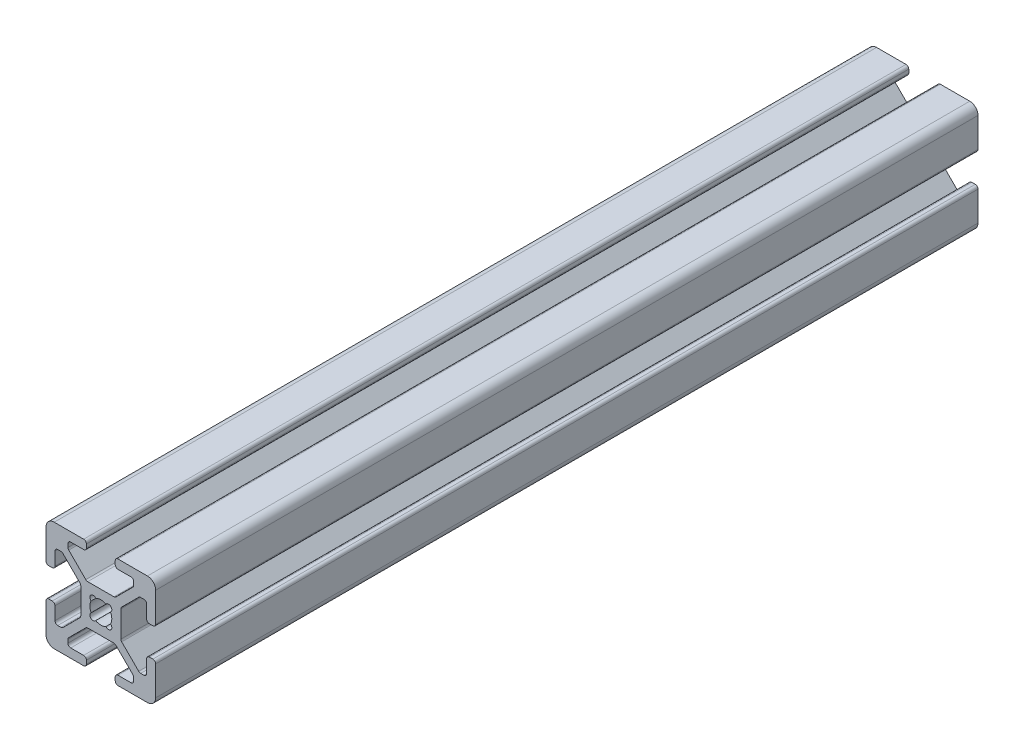
SolidWorks part; units mm, degrees
ref_plane "Front Plane" through (0, 0, 0) normal (0, 0, 1) x (1, 0, 0)
ref_plane "Top Plane" through (0, 0, 0) normal (0, 1, 0) x (1, 0, 0)
ref_plane "Right Plane" through (0, 0, 0) normal (1, 0, 0) x (0, 0, -1)
sketch "Sketch1" plane through (0, 0, 0) normal (0, 0, 1) x (1, 0, 0)
  line L0 (-2.7464, -3.807) -> (-5.848, -6.9086)
  line L1 (-8.5, -10) -> (-3.1319, -10)
  line L2 (-10, -8.5) -> (-10, -3.1319)
  line L3 (-8.5, 10) -> (-3.1319, 10)
  line L4 (10, -8.5) -> (10, -3.1319)
  line L6 (-10, 10) -> (-8.36, 8.36) construction
  line L7 (-2.3914, -3.66) -> (2.3914, -3.66)
  line L8 (-3.66, -2.3914) -> (-3.66, 2.3914)
  line L9 (-2.3914, 3.66) -> (2.3914, 3.66)
  line L10 (3.66, -2.3914) -> (3.66, 2.3914)
  line L13 (-5.4931, -8.36) -> (-3.1319, -8.36)
  line L14 (2.7464, -3.807) -> (5.848, -6.9086)
  line L15 (3.807, -2.7464) -> (6.9086, -5.848)
  line L16 (-5.995, -14.365) -> (5.995, -14.365)
  line L17 (2.63, -9.4981) -> (2.63, -8.8619)
  line L18 (8.8619, -2.63) -> (9.4981, -2.63)
  line L19 (5.995, -7.8581) -> (5.995, -7.2636)
  line L20 (-10, 3.1319) -> (-10, 8.5)
  line L22 (7.2636, -5.995) -> (7.8581, -5.995)
  line L23 (8.36, -5.4931) -> (8.36, -3.1319)
  line L24 (-3.807, -2.7464) -> (-6.9086, -5.848)
  line L25 (-9.4981, -2.63) -> (-8.8619, -2.63)
  line L26 (-7.8581, -5.995) -> (-7.2636, -5.995)
  line L27 (-5.995, -7.2636) -> (-5.995, -7.8581)
  line L28 (-2.63, -8.8619) -> (-2.63, -9.4981)
  line L30 (-5.4931, -8.36) -> (-3.1319, -8.36)
  line L31 (-3.807, 2.7464) -> (-6.9086, 5.848)
  line L32 (-2.7464, 3.807) -> (-5.848, 6.9086)
  line L33 (-2.63, 9.4981) -> (-2.63, 8.8619)
  line L34 (-5.995, 7.8581) -> (-5.995, 7.2636)
  line L35 (-7.2636, 5.995) -> (-7.8581, 5.995)
  line L36 (-8.8619, 2.63) -> (-9.4981, 2.63)
  line L37 (3.1319, 10) -> (8.5, 10)
  line L38 (-8.36, 5.4931) -> (-8.36, 3.1319)
  line L39 (2.7464, 3.807) -> (5.848, 6.9086)
  line L40 (3.807, 2.7464) -> (6.9086, 5.848)
  line L41 (9.4981, 2.63) -> (8.8619, 2.63)
  line L42 (7.8581, 5.995) -> (7.2636, 5.995)
  line L43 (5.995, 7.2636) -> (5.995, 7.8581)
  line L44 (2.63, 8.8619) -> (2.63, 9.4981)
  line L45 (8.36, -5.4931) -> (8.36, -3.1319)
  line L46 (5.4931, 8.36) -> (3.1319, 8.36)
  line L49 (-8.36, 5.4931) -> (-8.36, 3.1319)
  line L50 (5.4931, 8.36) -> (3.1319, 8.36)
  line L51 (-3.1319, 8.36) -> (-5.4931, 8.36)
  line L52 (-3.1319, 8.36) -> (-5.4931, 8.36)
  line L53 (10, 8.36) -> (8.36, 8.36) [skipped]
  line L54 (10, 3.1319) -> (10, 8.5)
  line L55 (8.36, 3.1319) -> (8.36, 5.4931)
  line L56 (8.36, 3.1319) -> (8.36, 5.4931)
  line L57 (3.1319, -8.36) -> (5.4931, -8.36)
  line L58 (3.1319, -8.36) -> (5.4931, -8.36)
  line L59 (3.1319, -10) -> (8.5, -10)
  line L60 (-8.36, -3.1319) -> (-8.36, -5.4931)
  line L61 (-8.36, -3.1319) -> (-8.36, -5.4931)
  line L62 (-8.36, 10) -> (-8.36, 8.36) [skipped]
  arc A0 (-8.5, -10) -> (-10, -8.5) centre (-8.5, -8.5) cw
  arc A1 (8.5, -10) -> (10, -8.5) centre (8.5, -8.5) ccw
  arc A2 (10, 8.5) -> (8.5, 10) centre (8.5, 8.5) ccw
  arc A3 (-8.5, 10) -> (-10, 8.5) centre (-8.5, 8.5) ccw
  arc A4 (10, -3.1319) -> (9.4981, -2.63) centre (9.4981, -3.1319) ccw
  arc A5 (8.8619, -2.63) -> (8.36, -3.1319) centre (8.8619, -3.1319) ccw
  arc A6 (7.8581, -5.995) -> (8.36, -5.4931) centre (7.8581, -5.4931) ccw
  arc A7 (7.2636, -5.995) -> (6.9086, -5.848) centre (7.2636, -5.4931) cw
  arc A8 (5.995, -7.2636) -> (5.848, -6.9086) centre (5.4931, -7.2636) ccw
  arc A9 (5.995, -7.8581) -> (5.4931, -8.36) centre (5.4931, -7.8581) cw
  arc A10 (3.1319, -10) -> (2.63, -9.4981) centre (3.1319, -9.4981) cw
  arc A11 (2.63, -8.8619) -> (3.1319, -8.36) centre (3.1319, -8.8619) cw
  arc A12 (-3.1319, -10) -> (-2.63, -9.4981) centre (-3.1319, -9.4981) ccw
  arc A13 (-2.63, -8.8619) -> (-3.1319, -8.36) centre (-3.1319, -8.8619) ccw
  arc A14 (-5.4931, -8.36) -> (-5.995, -7.8581) centre (-5.4931, -7.8581) cw
  arc A15 (-5.995, -7.2636) -> (-5.848, -6.9086) centre (-5.4931, -7.2636) cw
  arc A16 (-9.4981, -2.63) -> (-10, -3.1319) centre (-9.4981, -3.1319) ccw
  arc A17 (-8.36, -3.1319) -> (-8.8619, -2.63) centre (-8.8619, -3.1319) ccw
  arc A18 (-7.2636, -5.995) -> (-6.9086, -5.848) centre (-7.2636, -5.4931) ccw
  arc A19 (-7.8581, -5.995) -> (-8.36, -5.4931) centre (-7.8581, -5.4931) cw
  arc A20 (-3.807, -2.7464) -> (-3.66, -2.3914) centre (-4.1619, -2.3914) ccw
  arc A21 (-2.3914, -3.66) -> (-2.7464, -3.807) centre (-2.3914, -4.1619) ccw
  arc A22 (2.7464, -3.807) -> (2.3914, -3.66) centre (2.3914, -4.1619) ccw
  arc A23 (3.807, -2.7464) -> (3.66, -2.3914) centre (4.1619, -2.3914) cw
  arc A24 (9.4981, 2.63) -> (10, 3.1319) centre (9.4981, 3.1319) ccw
  arc A25 (8.8619, 2.63) -> (8.36, 3.1319) centre (8.8619, 3.1319) cw
  arc A26 (5.848, 6.9086) -> (5.995, 7.2636) centre (5.4931, 7.2636) ccw
  arc A27 (7.2636, 5.995) -> (6.9086, 5.848) centre (7.2636, 5.4931) ccw
  arc A28 (8.36, 5.4931) -> (7.8581, 5.995) centre (7.8581, 5.4931) ccw
  arc A29 (5.995, 7.8581) -> (5.4931, 8.36) centre (5.4931, 7.8581) ccw
  arc A30 (3.66, 2.3914) -> (3.807, 2.7464) centre (4.1619, 2.3914) cw
  arc A31 (-3.66, 2.3914) -> (-3.807, 2.7464) centre (-4.1619, 2.3914) ccw
  arc A32 (2.3914, 3.66) -> (2.7464, 3.807) centre (2.3914, 4.1619) ccw
  arc A33 (-2.3914, 3.66) -> (-2.7464, 3.807) centre (-2.3914, 4.1619) cw
  arc A34 (3.1319, 8.36) -> (2.63, 8.8619) centre (3.1319, 8.8619) cw
  arc A35 (2.63, 9.4981) -> (3.1319, 10) centre (3.1319, 9.4981) cw
  arc A36 (-9.4981, 2.63) -> (-10, 3.1319) centre (-9.4981, 3.1319) cw
  arc A37 (-8.8619, 2.63) -> (-8.36, 3.1319) centre (-8.8619, 3.1319) ccw
  arc A38 (-3.1319, 8.36) -> (-2.63, 8.8619) centre (-3.1319, 8.8619) ccw
  arc A39 (-2.63, 9.4981) -> (-3.1319, 10) centre (-3.1319, 9.4981) ccw
  arc A40 (-5.848, 6.9086) -> (-5.995, 7.2636) centre (-5.4931, 7.2636) cw
  arc A41 (-5.4931, 8.36) -> (-5.995, 7.8581) centre (-5.4931, 7.8581) ccw
  arc A42 (-6.9086, 5.848) -> (-7.2636, 5.995) centre (-7.2636, 5.4931) ccw
  arc A43 (-7.8581, 5.995) -> (-8.36, 5.4931) centre (-7.8581, 5.4931) ccw
  arc A44 (-1.7677, 0.9356) -> (-1.7677, -0.9356) centre (0, 0) ccw
  arc A45 (-0.9356, 1.7677) -> (-1.7677, 0.9356) centre (-1.4142, 1.4142) ccw
  arc A46 (1.7677, 0.9356) -> (0.9356, 1.7677) centre (1.4142, 1.4142) ccw
  arc A47 (0.9356, -1.7677) -> (1.7677, -0.9356) centre (1.4142, -1.4142) ccw
  arc A48 (-1.7677, -0.9356) -> (-0.9356, -1.7677) centre (-1.4142, -1.4142) ccw
  arc A49 (-0.9356, -1.7677) -> (0.9356, -1.7677) centre (0, 0) ccw
  arc A50 (1.7677, -0.9356) -> (1.7677, 0.9356) centre (0, 0) ccw
  arc A51 (0.9356, 1.7677) -> (-0.9356, 1.7677) centre (0, 0) ccw
  point P0 (0, 0)
  point P5 (0, 0)
  point P9 (-10, -10)
  point P11 (0, -10)
  point P14 (0, -3.66)
  point P23 (3.66, 0)
  point P66 (0, 0)
  point P70 (0, 0)
  dimension "D2" = 1.5
  dimension "D5" = 0.5019
  dimension "D6" = 4
  dimension "D7" = 1.19
  dimension "D1" = 20
  dimension "D3" = 11.99
  dimension "D4" = 4
  dimension "D8" = 4
extrude "Boss-Extrude1" add sketch "Sketch1" along normal blind 150 contours A43 L35 A42 L31 A31 L8 A20 L24 A18 L26 A19 L60 A17 L25 A16 L2 A0 L1 A12 L28 A13 L13 A14 L27 A15 L0 A21 L7 A22 L14 A8 L19 A9 L57 A11 L17 A10 L59 A1 L4 A4 L18 A5 L23 A6 L22 A7 L15 A23 L10 A30
